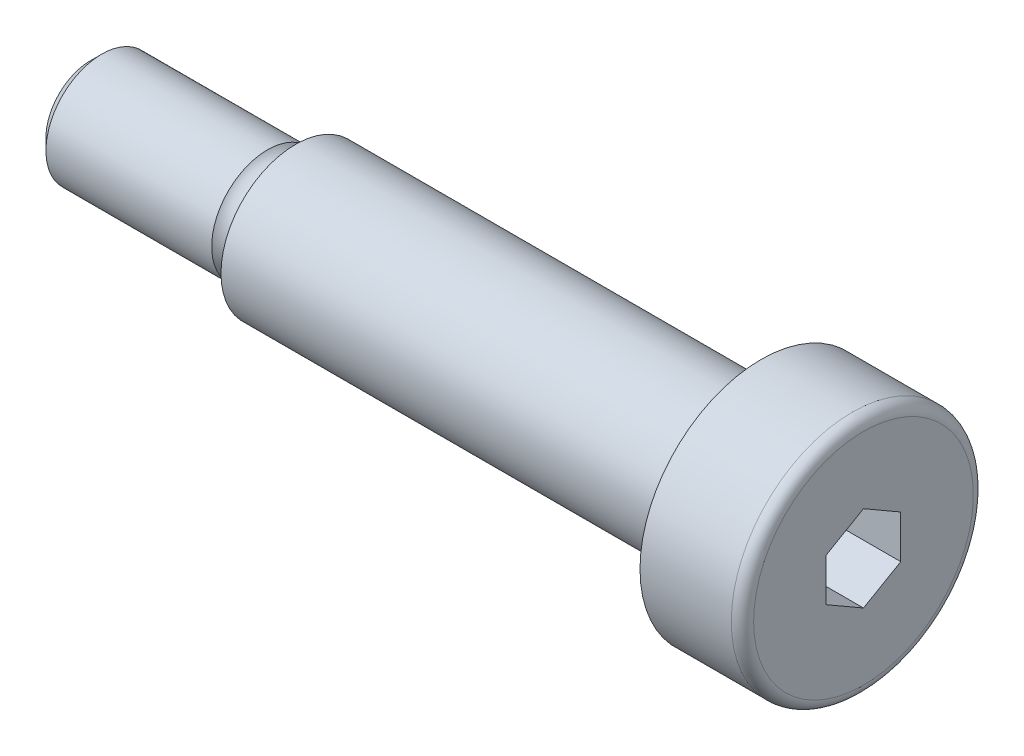
SolidWorks part; units mm, degrees
material "1.0503 (C45)"
ref_plane "Płaszczyzna XY" through (0, 0, 0) normal (0, 0, 1) x (1, 0, 0)
ref_plane "Płaszczyzna XZ" through (0, 0, 0) normal (0, 1, 0) x (1, 0, 0)
ref_plane "Płaszczyzna YZ" through (0, 0, 0) normal (1, 0, 0) x (0, 0, -1)
sketch "Śruba parametryczna" plane through (0, 0, 0) normal (0, 0, 1) x (1, 0, 0)
  line L0 (0, 0) -> (0, 6.5)
  line L1 (0, 6.5) -> (-5.5, 6.5)
  line L2 (-5.5, 6.5) -> (-5.5, 4)
  line L3 (-5.5, 4) -> (-30.5, 4)
  line L4 (-30.5, 4) -> (-30.5, 3)
  line L5 (-30.5, 3) -> (-41.5, 3)
  line L6 (-41.5, 3) -> (-41.5, 0)
  line L7 (-41.5, 0) -> (0, 0)
  line L8 (0, 0) -> (5.7531, 0) construction
  dimension "d3" = 13
  dimension "d1" = 8
  dimension "l3" = 5.5
  dimension "l1" = 25
  dimension "l2" = 11
  dimension "d2" = 6
revolve "Obrót1" add sketch "Śruba parametryczna" angle 360 about L8
fillet "Zaokrąglenie1" radius 0.6 1 edges at (0, 0, 6.5)
chamfer "Sfazowanie1" distance 0.6 1 edges at (-41.5, 0, 3)
sketch "Szkic2" plane through (0, 0, 0) normal (1, 0, 0) x (0, 0, -1)
  line L1 (-2, -1.1547) -> (0, -2.3094)
  line L2 (0, -2.3094) -> (2, -1.1547)
  line L3 (2, -1.1547) -> (2, 1.1547)
  line L4 (2, 1.1547) -> (0, 2.3094)
  line L5 (0, 2.3094) -> (-2, 1.1547)
  line L6 (-2, 1.1547) -> (-2, -1.1547)
  circle A0 centre (0, 0) radius 2 construction
  dimension "A/F" = 4
extrude "Wytnij-wyciągnięcie1" cut sketch "Szkic2" against normal blind 5
sketch "Szkic3" plane through (0, 0, 0) normal (0, 1, 0) x (1, 0, 0)
  line L2 (-40.9, -3) -> (-30.5, -3) construction
  line L3 (-32, -3) -> (-30.5, -3)
  line L4 (3.8052, 0) -> (-51.1335, 0) construction
  arc A1 (-30.5, -3) -> (-32, -3) centre (-31.25, -3.6614) ccw
  dimension "D1" = 1
  dimension "D2" = 1.5
revolve "Wycięcie-obrót1" cut sketch "Szkic3" angle 360 about L4
